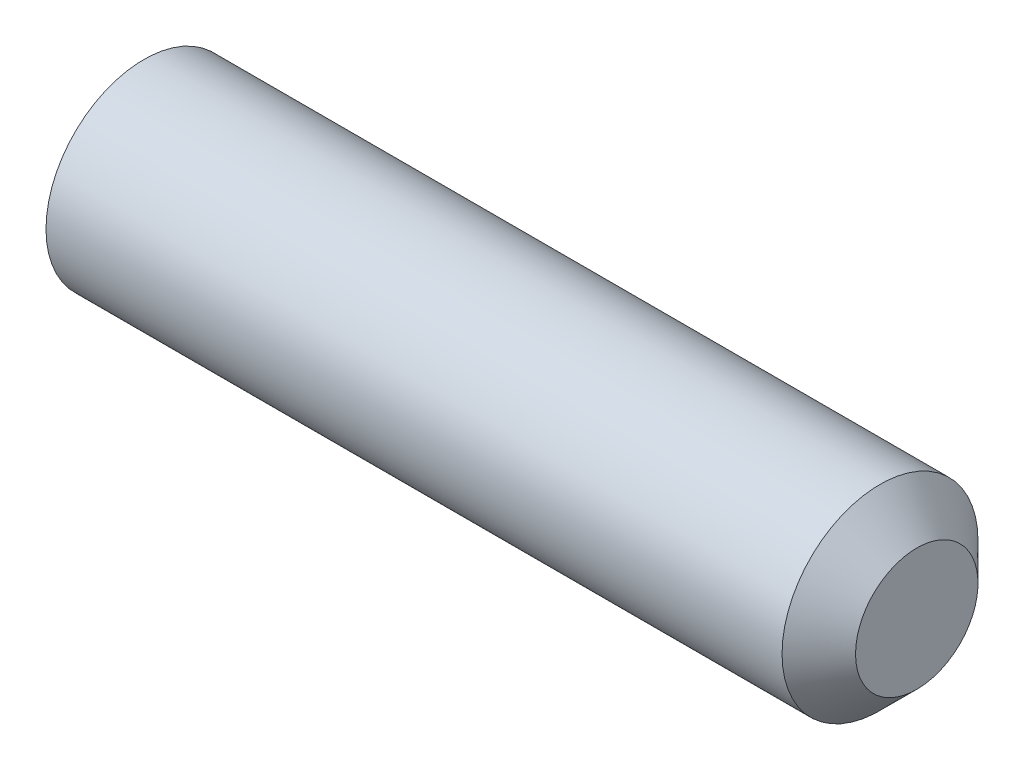
SolidWorks part; units mm, degrees
ref_plane "Plane1" through (0, 0, 0) normal (0, 0, 1) x (1, 0, 0)
ref_plane "Plane2" through (0, 0, 0) normal (0, 1, 0) x (1, 0, 0)
ref_plane "Plane3" through (0, 0, 0) normal (1, 0, 0) x (0, 0, -1)
sketch "BodySke" plane through (0, 0, 0) normal (0, 0, 1) x (1, 0, 0)
  line L0 (0, 0) -> (0, 1.61)
  line L1 (0, 1.61) -> (0.2252, 2)
  line L2 (0.2252, 2) -> (15.25, 2)
  line L3 (15.25, 2) -> (16, 1.25)
  line L4 (16, 0) -> (0, 0)
  line L5 (-12.7, 0) -> (88.9, 0) construction
  line L6 (16, 1.25) -> (16, 0)
  line L7 (16, 1.25) -> (16, 10.775) construction
  line L8 (0, -1.61) -> (0.2252, -2) construction
  line L9 (0.7, 15.875) -> (0.7, -3.175) construction
  line L10 (15.25, -2) -> (16, -1.25) construction
  dimension "Length" = 16
  dimension "Diameter" = 4
  dimension "Drive_ch_ang" = 60
  dimension "Minor_dia" = 3.22
  dimension "Cup_nose_ang" = 45
  dimension "Cup_dia" = 2.5
  dimension "Advance" = 0.7
revolve "BaseBody" add sketch "BodySke" angle 360 about L5
cosmetic thread "ThreadCosmetic" [suppressed] parameters "Thread_minor"=3.22
sketch "Sketch2" plane through (0, 0, 0) normal (-1, 0, 0) x (0, 0, 1)
  line L0 (0.5774, 1) -> (-0.5774, 1)
  line L1 (-0.5774, 1) -> (-1.1547, 0)
  line L2 (0.5774, 1) -> (1.1547, 0)
  line L3 (0.5774, -1) -> (1.1547, 0)
  line L4 (0.5774, -1) -> (-0.5774, -1)
  line L5 (-0.5774, -1) -> (-1.1547, 0)
  dimension "Hex_size" = 2
  dimension "D2" = 1
  dimension "D3" = 1
extrude "Hex" cut sketch "Sketch2" against normal blind 2.5
sketch "ThdSchSke" plane through (0, 0, 0) normal (0, 0, 1) x (1, 0, 0)
  line L0 (0.2252, -1.61) -> (-0.0479, -2)
  line L1 (0.2252, -1.61) -> (0.4982, -2)
  line L2 (0.4982, -2) -> (0.4982, -2.5)
  line L3 (-3.175, 0) -> (5.1513, 0) construction
  line L5 (0.4982, -2.5) -> (-0.0479, -2.5)
  line L6 (-0.0479, -2.5) -> (-0.0479, -2)
  line L8 (0.2252, 2) -> (0.2252, -2) construction
  dimension "Thread_minor" = 3.22
  dimension "Diameter" = 4
  dimension "SideAngle" = 55
  dimension "VeeAngle" = 70
  dimension "Overcut" = 5
revolve "ThreadSchematic" [suppressed] cut sketch "ThdSchSke" angle 360 about L3
pattern_linear "ThdSchPat" [suppressed]
equation "\"D2@Sketch2\" = \"Hex_size@Sketch2\" / 2"
equation "\"D3@Sketch2\" = \"Hex_size@Sketch2\" / 2"
equation "\"Thread_minor@ThreadCosmetic\" = \"Minor_dia@BodySke\""
equation "\"Thread_minor@ThdSchSke\" = \"Thread_minor@ThreadCosmetic\""
equation "\"Diameter@ThdSchSke\" = \"Diameter@BodySke\""
equation "\"Overcut@ThdSchSke\" = \"Diameter@BodySke\" * 1.25"
equation "\"Num_threads@ThdSchPat\" = int( (\"Length@BodySke\" - ( ( ( \"Diameter@BodySke\" - \"Minor_dia@BodySke\" ) * 0.5 ) / tan( \"Drive_ch_ang@BodySke\" * 0.017453292 ) ) - ( ( ( \"Diameter@BodySke\" - \"Cup_dia@BodySke\" ) * 0.5 ) * tan( \"Cup_nose_ang@BodySke\" * 0.017453292 ) ) ) / \"Advance@BodySke\" + 0.999 )  + 1"
equation "\"Advance@ThdSchPat\" = (\"Length@BodySke\" - ( ( ( \"Diameter@BodySke\" - \"Minor_dia@BodySke\" ) * 0.5 ) / tan( \"Drive_ch_ang@BodySke\" * 0.017453292 ) ) - ( ( ( \"Diameter@BodySke\" - \"Cup_dia@BodySke\" ) * 0.5 ) * tan( \"Cup_nose_ang@BodySke\" * 0.017453292 ) ) ) /  (\"Num_threads@ThdSchPat\" - 1) 'relax it"
equation "' \"Num_threads@ThdSchPat\" = \"Num_threads@ThdSchPat\" - sgn( \"Num_threads@ThdSchPat\" - 1) '---chamfered tips only---"
